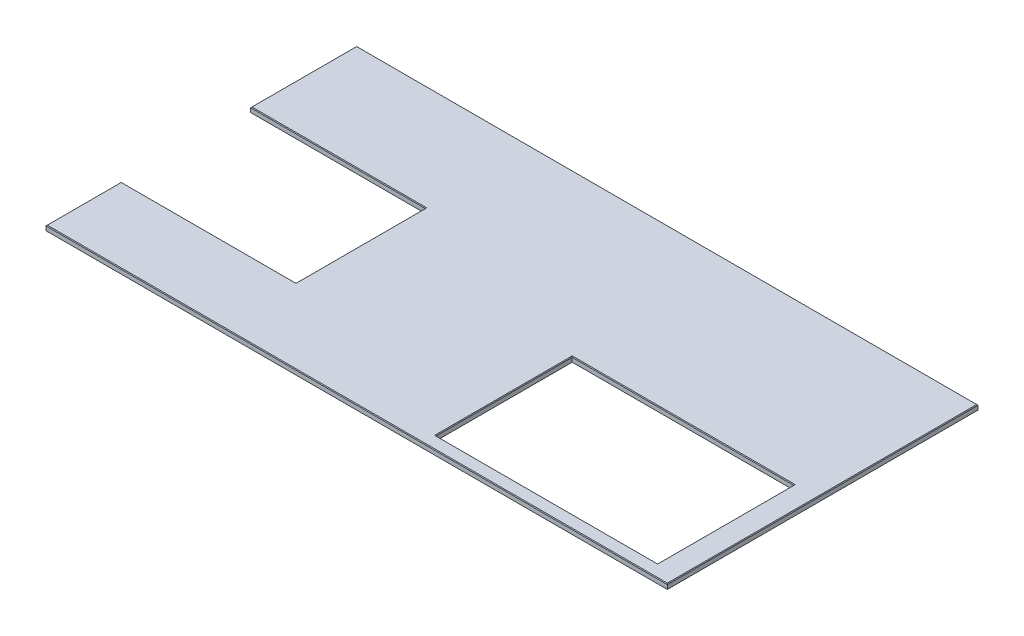
SolidWorks part; units mm, degrees
material "Oak"
ref_plane "Front Plane" through (0, 0, 0) normal (0, 0, 1) x (1, 0, 0)
ref_plane "Top Plane" through (0, 0, 0) normal (0, 1, 0) x (1, 0, 0)
ref_plane "Right Plane" through (0, 0, 0) normal (1, 0, 0) x (0, 0, -1)
sketch "Sketch1" plane through (0, 0, 0) normal (0, 1, 0) x (1, 0, 0)
  line L0 (1479.4865, 50.8) -> (1479.4865, 585.724)
  line L1 (1479.4865, 585.724) -> (2349.4365, 585.724)
  line L2 (2349.4365, 585.724) -> (2349.4365, 50.8)
  line L4 (2438.4, 0) -> (2438.4, 1219.2)
  line L5 (2438.4, 1219.2) -> (0, 1219.2)
  line L6 (0, 1219.2) -> (0, 803.275)
  line L7 (0, 0) -> (2438.4, 0)
  line L8 (0, 295.275) -> (0, 0)
  line L9 (0, 803.275) -> (685.8, 803.275)
  line L11 (0, 295.275) -> (685.8, 295.275)
  line L12 (685.8, 803.275) -> (685.8, 295.275)
  line L14 (1479.4865, 50.8) -> (2349.4365, 50.8)
  dimension "D1" = 2438.4
  dimension "D2" = 1479.4865
  dimension "D3" = 869.95
  dimension "D4" = 534.924
  dimension "D5" = 1219.2
  dimension "D6" = 685.8
  dimension "D7" = 295.275
  dimension "D8" = 415.925
  dimension "D9" = 50.8
extrude "Boss-Extrude1" add sketch "Sketch1" against normal blind 19.05
chamfer "Chamfer1" distance 2.54 angle 45 12 edges at (0, 0, -1011.2375) (1219.2, 0, -1219.2) (2438.4, 0, -609.6) (2349.4365, 0, -318.262) (1914.4615, 0, -585.724) (1479.4865, 0, -318.262) (1219.2, 0, 0) (0, 0, -147.6375) (342.9, 0, -295.275) (685.8, 0, -549.275) (342.9, 0, -803.275) (1914.4615, 0, -50.8)
